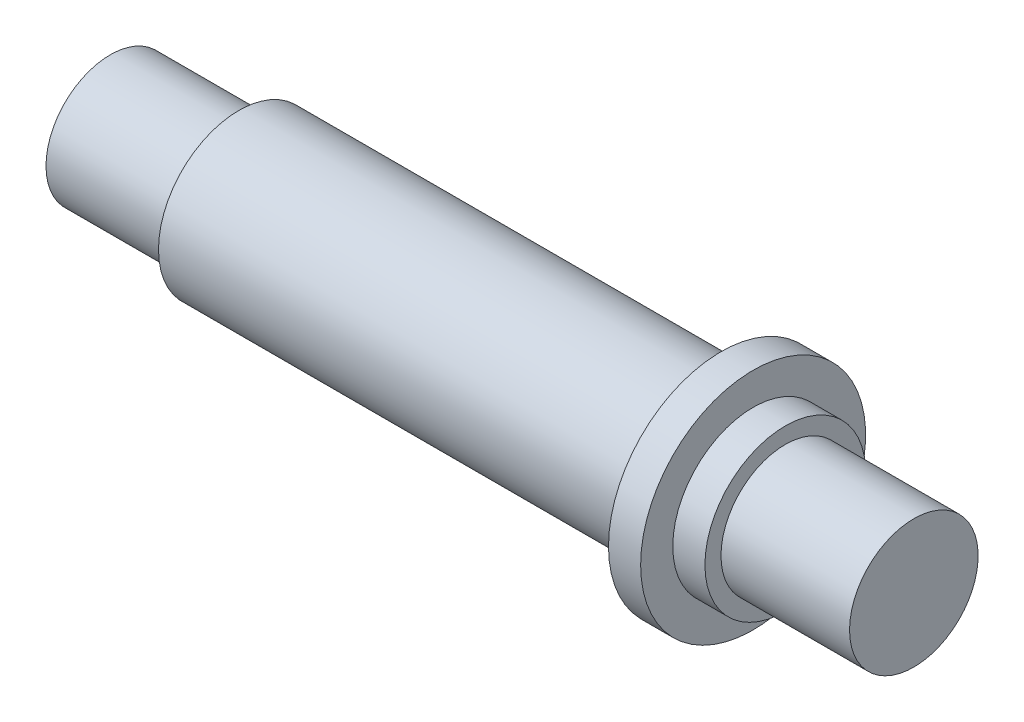
SolidWorks part; units mm, degrees
material "普通碳钢"
ref_plane "前视基准面" through (0, 0, 0) normal (0, 0, 1) x (1, 0, 0)
ref_plane "上视基准面" through (0, 0, 0) normal (0, 1, 0) x (1, 0, 0)
ref_plane "右视基准面" through (0, 0, 0) normal (1, 0, 0) x (0, 0, -1)
sketch "草图1" plane through (0, 0, 0) normal (0, 0, 1) x (1, 0, 0)
  line L0 (-56.4792, 0) -> (46.1737, 0) construction
  line L1 (-45.1545, 0) -> (-45.1545, 2)
  line L2 (-45.1545, 2) -> (-41.1545, 2)
  line L3 (-41.1545, 2) -> (-41.1545, 2.5)
  line L4 (-41.1545, 2.5) -> (-26.1545, 2.5)
  line L5 (-26.1545, 2.5) -> (-26.1545, 3.5)
  line L6 (-26.1545, 3.5) -> (-25.1545, 3.5)
  line L7 (-25.1545, 3.5) -> (-25.1545, 2.5)
  line L8 (-25.1545, 2.5) -> (-24.1545, 2.5)
  line L9 (-24.1545, 2.5) -> (-24.1545, 2)
  line L10 (-24.1545, 2) -> (-20.1545, 2)
  line L11 (-20.1545, 2) -> (-20.1545, 0)
  line L12 (-45.1545, 0) -> (-20.1545, 0)
  dimension "D1" = 2
  dimension "D2" = 4
  dimension "D3" = 15
  dimension "D4" = 1
  dimension "D5" = 1
  dimension "D6" = 4
  dimension "D7" = 5
  dimension "D8" = 7
  dimension "D9" = 1
  dimension "D10" = 0.5
revolve "旋转1" add sketch "草图1" angle 360 about L0
